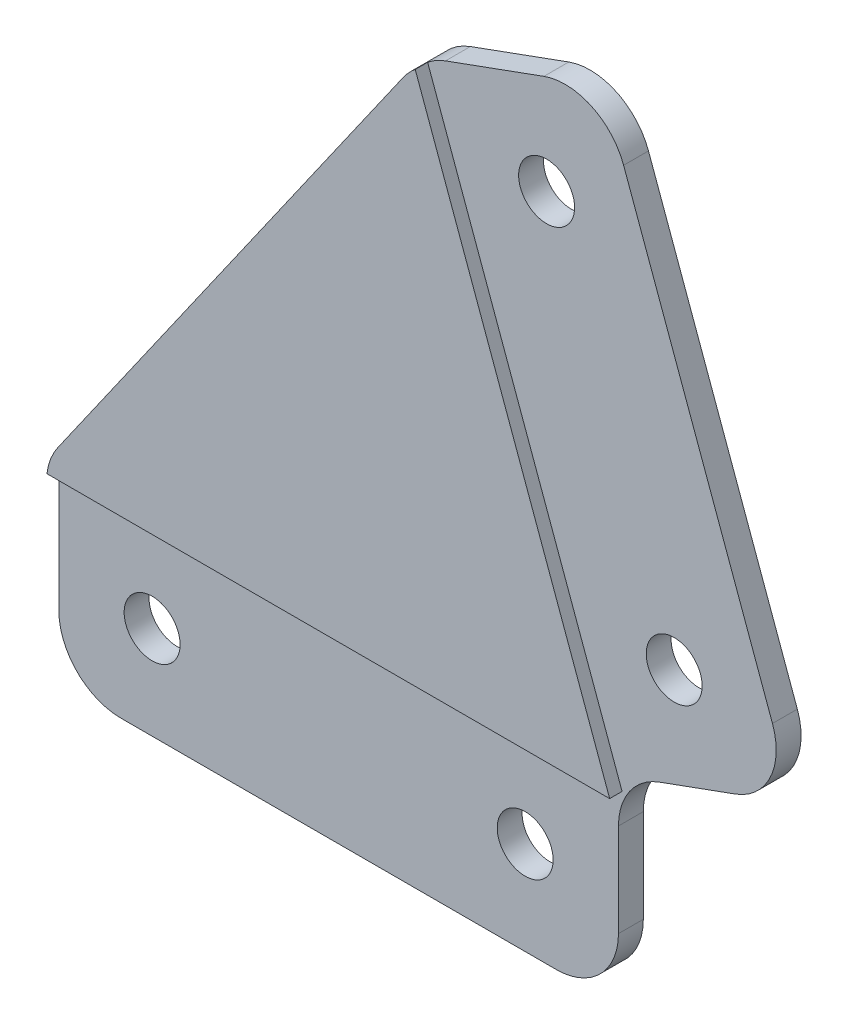
SolidWorks part; units mm, degrees
material "3.1325 (EN-AW 2017A)"
ref_plane "正面" through (0, 0, 0) normal (0, 0, 1) x (1, 0, 0)
ref_plane "平面" through (0, 0, 0) normal (0, 1, 0) x (1, 0, 0)
ref_plane "右側面" through (0, 0, 0) normal (1, 0, 0) x (0, 0, -1)
sketch "ｽｹｯﾁ1" plane through (0, 0, 0) normal (0, 0, 1) x (1, 0, 0)
  line L0 (0, 0) -> (306.8848, 365.731) construction
  line L1 (306.8848, 365.731) -> (440, 0) construction
  line L2 (440, 0) -> (0, 0) construction
  line L3 (306.8848, 365.731) -> (306.8848, 0) construction
  line L4 (306.8848, 365.731) -> (0, 0) construction
  line L9 (306.8848, 365.731) -> (295.3941, 375.3729)
  line L20 (440, 0) -> (395, 0)
  line L21 (440, 0) -> (440, -16)
  line L22 (395, 0) -> (395, -16)
  line L23 (440, -16) -> (395, -16)
  line L24 (440, 0) -> (424.6091, 42.2862)
  line L25 (440, 0) -> (454.0954, 5.1303)
  line L26 (424.6091, 42.2862) -> (438.7045, 47.4165)
  line L27 (454.0954, 5.1303) -> (438.7045, 47.4165)
  line L28 (424.6091, 42.2862) -> (395, 0)
  dimension "D4" = 16
  dimension "D5" = 15
  dimension "D6" = 45
  dimension "D1" = 440
  dimension "D2" = 70
  dimension "D3" = 50
  dimension "D7" = 45
extrude "ﾎﾞｽ - 押し出し1" add sketch "ｽｹｯﾁ1" along normal blind 3
sketch "ｽｹｯﾁ2" plane through (0, 0, 3) normal (0, 0, 1) x (1, 0, 0)
  line L6 (440, -16) -> (395, -16) construction
  line L7 (395, 0) -> (395, -16) construction
  line L8 (440, 0) -> (454.0954, 5.1303) construction
  line L9 (424.6091, 42.2862) -> (438.7045, 47.4165) construction
  line L10 (454.0954, 5.1303) -> (438.7045, 47.4165) construction
  circle A4 centre (402.5, -8.5) radius 2.25
  circle A5 centre (432.5, -8.5) radius 2.25
  circle A6 centre (434.2219, 37.8036) radius 2.25
  circle A7 centre (444.4825, 9.6128) radius 2.25
  dimension "D1" = 4.5
  dimension "D2" = 4.5
  dimension "D3" = 4.5
  dimension "D4" = 4.5
  dimension "D5" = 7.5
  dimension "D6" = 7.5
  dimension "D7" = 7.5
  dimension "D8" = 30
  dimension "D9" = 7.5
  dimension "D10" = 7.5
  dimension "D11" = 7.5
  dimension "D12" = 7.5
extrude "ｶｯﾄ - 押し出し1" cut sketch "ｽｹｯﾁ2" against normal blind 3
fillet "ﾌｨﾚｯﾄ1" radius 5 7 edges at (454.0954, 5.1303, 1.5) (440, -16, 1.5) (440, 0, 1.5) (395, -16, 1.5) (438.7045, 47.4165, 1.5) (424.6091, 42.2862, 1.5) (395, 0, 1.5)
sketch "ｽｹｯﾁ4" plane through (0, 0, 3) normal (0, 0, 1) x (1, 0, 0)
  line L8 (438.7045, 47.4165) -> (455.1214, 2.3112)
  line L9 (438.7045, 47.4165) -> (424.5621, 42.2691)
  line L10 (455.1214, 2.3112) -> (443, -2.1006)
  line L11 (424.5621, 42.2691) -> (440.2926, -0.95)
  line L12 (452.3853, 9.8288) -> (440.4146, 42.718) construction
  line L13 (443, -16) -> (395, -16)
  line L14 (443, -16) -> (443, -2.1006)
  line L15 (395, -16) -> (395, -0.95)
  line L16 (440.2926, -0.95) -> (395, -0.95)
  line L17 (435, -16) -> (400, -16) construction
  line L19 (426.0905, 42.8254) -> (434.006, 45.7064) construction
  line L20 (395, -1.5765) -> (395, -11) construction
  line L22 (443.2899, 1.1974) -> (449.3969, 3.4202) construction
  line L23 (440, -3.501) -> (440, -11) construction
  line L24 (443, -0.95) -> (440.2926, -0.95) construction
  line L25 (440.2926, -0.95) -> (440.9791, -2.8362) construction
  line L26 (443, -2.1006) -> (440.9791, -2.8362) construction
  line L27 (443, -2.1006) -> (443, -0.95) construction
  dimension "D1" = 15.05
  dimension "D2" = 15.05
  dimension "D3" = 3
  dimension "D4" = 3
extrude "ｶｯﾄ - 押し出し2" cut sketch "ｽｹｯﾁ4" against normal blind 1
